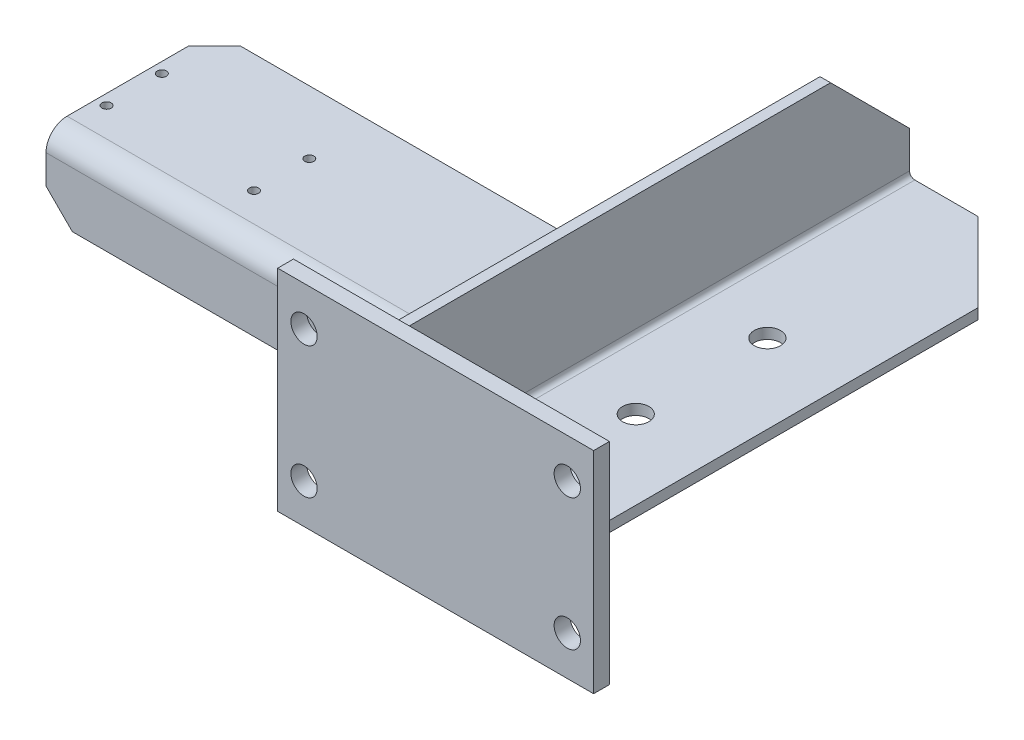
SolidWorks part; units mm, degrees
ref_plane "前视基准面" through (0, 0, 0) normal (0, 0, 1) x (1, 0, 0)
ref_plane "上视基准面" through (0, 0, 0) normal (0, 1, 0) x (1, 0, 0)
ref_plane "右视基准面" through (0, 0, 0) normal (1, 0, 0) x (0, 0, -1)
sketch "草图1" plane through (0, 0, 0) normal (0, 0, 1) x (1, 0, 0)
  line L0 (0, 6) -> (0, 50)
  line L1 (6, 0) -> (60, 0)
  line L2 (6, 4) -> (60, 4)
  line L3 (4, 6) -> (4, 50)
  line L4 (4, 50) -> (0, 50)
  line L5 (60, 4) -> (60, 0)
  arc A0 (0, 6) -> (6, 0) centre (6, 6) ccw
  arc A1 (4, 6) -> (6, 4) centre (6, 6) ccw
  point P6 (0, 0)
  dimension "D3" = 6
  dimension "D1" = 50
  dimension "D2" = 60
  dimension "D4" = 4
extrude "凸台-拉伸1" add sketch "草图1" along normal blind 200
sketch "草图2" plane through (0, 0, 200) normal (0, 0, 1) x (1, 0, 0)
  line L1 (90, 60) -> (-30, 60)
  line L2 (90, 60) -> (90, -20)
  line L3 (90, -20) -> (-30, -20)
  line L4 (-30, 60) -> (-30, -20)
  line L5 (4, 50) -> (0, 50) construction
  line L6 (-30, 20) -> (90, 20) construction
  line L7 (30, 60) -> (30, -20) construction
  line L8 (-30, -5) -> (90, -5) construction
  line L9 (-30, 45) -> (90, 45) construction
  line L10 (-20, 60) -> (-20, -20) construction
  line L11 (80, 60) -> (80, -20) construction
  line L13 (0, 50) -> (0, 6) construction
  circle A0 centre (-20, 45) radius 5
  circle A1 centre (80, 45) radius 5
  circle A2 centre (-20, -5) radius 5
  circle A3 centre (80, -5) radius 5
  point P28 (2, 50)
  dimension "D7" = 10
  dimension "D1" = 80
  dimension "D2" = 120
  dimension "D3" = 25
  dimension "D5" = 10
  dimension "D6" = 10
  dimension "D8" = 10
  dimension "D9" = 30
  dimension "D4" = 25
extrude "凸台-拉伸2" add sketch "草图2" along normal blind 6 separate body
chamfer "倒角1" distance 30 angle 45 2 edges at (2, 50, 0) (60, 2, 0)
sketch "草图3" plane through (0, 4, 0) normal (0, 1, 0) x (1, 0, 0)
  line L0 (30, -130) -> (30, -80) construction
  line L1 (60, -200) -> (6, -200) construction
  line L2 (60, -200) -> (60, -30) construction
  circle A0 centre (30, -130) radius 5
  circle A1 centre (30, -80) radius 5
  dimension "D1" = 10
  dimension "D2" = 10
  dimension "D3" = 50
  dimension "D4" = 70
  dimension "D5" = 30
extrude "切除-拉伸1" cut sketch "草图3" against normal up to next (4 mm away)
sketch "草图4" plane through (0, 0, 0) normal (-1, 0, 0) x (0, 0, 1)
  line L0 (179, 6) -> (175, 6)
  line L2 (175, 6) -> (175, 27)
  line L3 (171, 31) -> (115, 31)
  line L4 (200, 60) -> (200, -20) construction
  line L5 (179, 2) -> (179, 31.3175) construction
  line L6 (179, 6) -> (179, 27)
  line L7 (171, 35) -> (115, 35)
  line L8 (149.8495, 2) -> (179, 2) construction
  line L9 (115, 35) -> (115, 31)
  line L10 (200, 0) -> (0, 0) construction
  line L11 (149.8495, 6) -> (175, 6) construction
  line L13 (200, 6) -> (0, 6) construction
  line L14 (172.5033, 35) -> (115, 35) construction
  line L15 (170.1985, 31) -> (115, 31) construction
  line L16 (175, 6) -> (175, 27.6618) construction
  arc A2 (175, 27.6618) -> (170.1985, 31) centre (177.9192, 36.9828) cw construction
  arc A3 (179, 31.3175) -> (172.5033, 35) centre (177.9192, 36.9828) cw construction
  arc A4 (171, 35) -> (179, 27) centre (171, 27) cw
  arc A5 (171, 31) -> (175, 27) centre (171, 27) cw
  dimension "D3" = 8
  dimension "D6" = 4
  dimension "D1" = 35
  dimension "D2" = 25
  dimension "D5" = 60
  dimension "D4" = 4
extrude "凸台-拉伸3" add sketch "草图4" along normal blind 145
chamfer "倒角2" distance 10 angle 45 2 edges at (-145, 33, 115) (-145, 6, 177)
sketch "草图7" plane through (0, 31, 0) normal (0, -1, 0) x (1, 0, 0)
  line L0 (-141, 160) -> (-83.25, 160) construction
  line L1 (-85, 161.75) -> (-85, 137.25) construction
  line L2 (-83.25, 139) -> (-142.75, 139) construction
  line L3 (-141, 137.25) -> (-141, 161.75) construction
  line L4 (-145, 125) -> (-145, 171) construction
  line L5 (-145, 179) -> (0, 179) construction
  circle A0 centre (-141, 160) radius 1.75
  circle A1 centre (-141, 139) radius 1.75
  circle A2 centre (-85, 139) radius 1.75
  circle A3 centre (-85, 160) radius 1.75
  dimension "D1" = 21
  dimension "D5" = 3.5
  dimension "D2" = 56
  dimension "D3" = 4
  dimension "D4" = 19
extrude "切除-拉伸2" cut sketch "草图7" against normal up to next (4 mm away)
